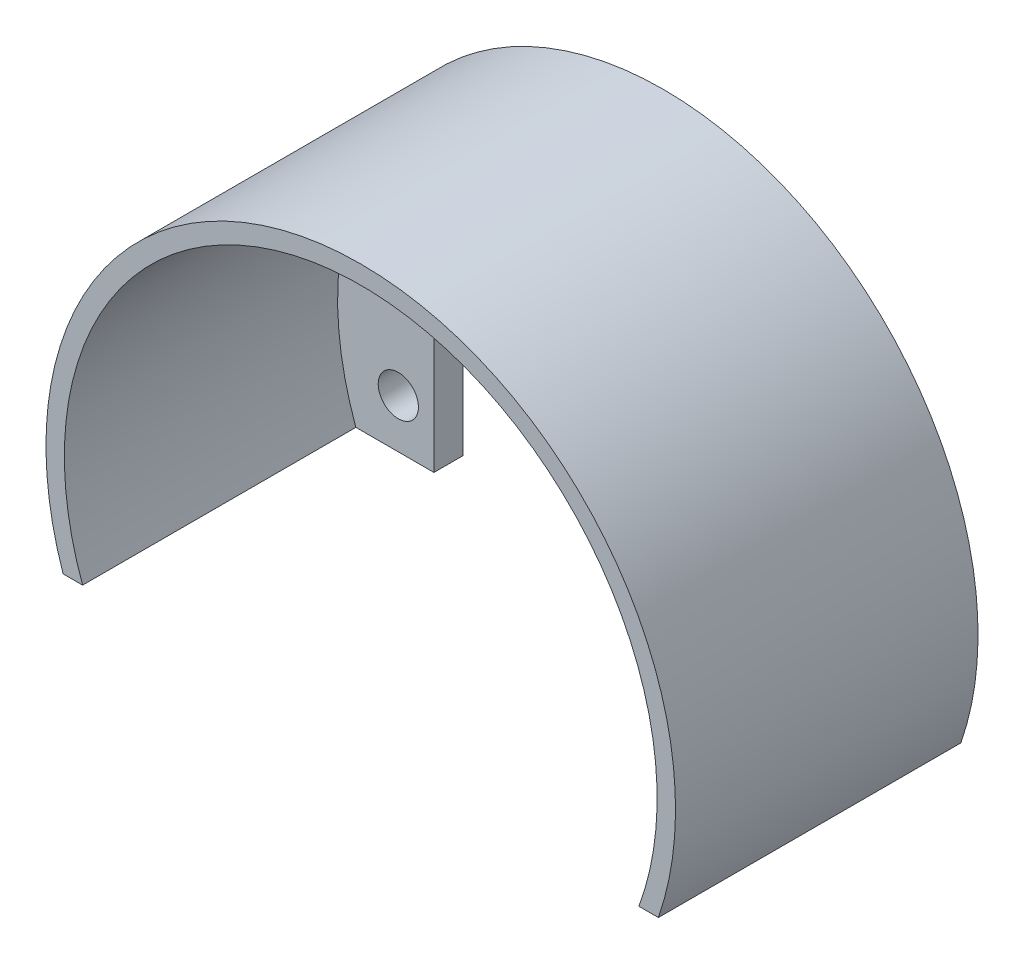
SolidWorks part; units mm, degrees
ref_plane "Alzado" through (0, 0, 0) normal (0, 0, 1) x (1, 0, 0)
ref_plane "Planta" through (0, 0, 0) normal (0, 1, 0) x (1, 0, 0)
ref_plane "Vista lateral" through (0, 0, 0) normal (1, 0, 0) x (0, 0, -1)
sketch "Croquis1" plane through (0, 0, 0) normal (0, 0, 1) x (1, 0, 0)
  line L0 (-17.6448, 11.6516) -> (23.3552, 11.6516) construction
  line L1 (2.8552, 1.1516) -> (2.8552, 43.9084) construction
  line L2 (-17.6448, 22.1516) -> (23.3552, 22.1516)
  line L3 (-17.6448, 1.1516) -> (23.3552, 1.1516) construction
  line L4 (-17.6448, 22.1516) -> (-17.6448, 1.1516)
  line L5 (-17.6448, 1.1516) -> (-27.6448, 1.1516)
  line L6 (23.3552, 1.1516) -> (33.3552, 1.1516)
  line L7 (23.3552, 22.1516) -> (23.3552, 1.1516)
  line L8 (30.3411, 11.1516) -> (-24.2133, 11.1516) construction
  arc A0 (-27.6448, 1.1516) -> (33.3552, 1.1516) centre (2.8552, 11.6516) cw
  circle A1 centre (27.0052, 6.1516) radius 2.0609
  circle A2 centre (-21.2948, 6.1516) radius 2.0609
  circle A3 centre (-21.2948, 16.1516) radius 2.0609
  circle A4 centre (27.0052, 16.1516) radius 2.0609
  point P20 (2.8552, 1.1516)
  dimension "D3" = 48.3
  dimension "D6" = 10
  dimension "D1" = 41
  dimension "D2" = 10
  dimension "D4" = 10
  dimension "D5" = 21
extrude "Saliente-Extruir1" add sketch "Croquis1" along normal blind 3
sketch "Croquis2" plane through (0, 0, 3) normal (0, 0, 1) x (1, 0, 0)
  line L0 (23.3552, 1.1516) -> (33.3552, 1.1516) construction
  line L1 (-27.6448, 1.1516) -> (-25.6448, 1.1516)
  line L2 (-27.6448, 1.1516) -> (-17.6448, 1.1516) construction
  line L3 (31.3552, 1.1516) -> (33.3552, 1.1516)
  arc A0 (-27.6448, 1.1516) -> (33.3552, 1.1516) centre (2.8552, 11.6516) cw
  arc A1 (-25.6448, 1.1516) -> (31.3552, 1.1516) centre (2.8552, 11.6516) cw
  dimension "D1" = 2
  dimension "D2" = 57
extrude "Saliente-Extruir2" add sketch "Croquis2" along normal blind 28
